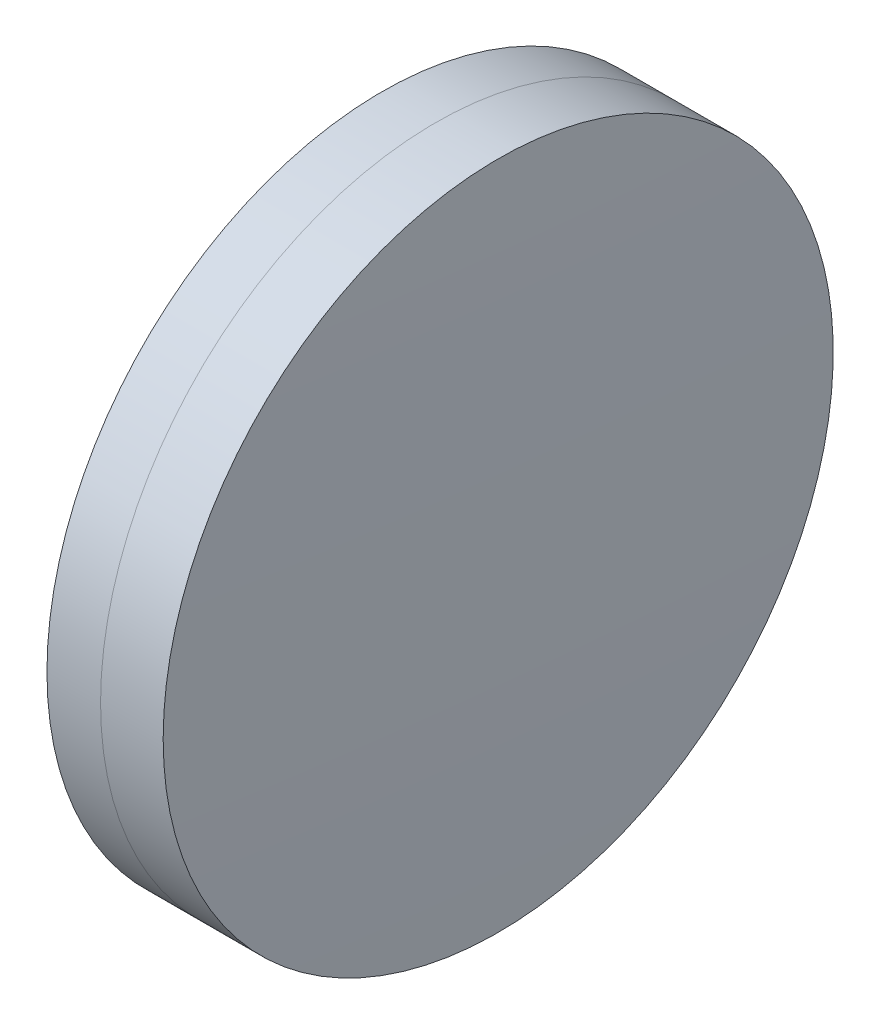
SolidWorks part; units mm, degrees
ref_plane "前视基准面" through (0, 0, 0) normal (0, 0, 1) x (1, 0, 0)
ref_plane "上视基准面" through (0, 0, 0) normal (0, 1, 0) x (1, 0, 0)
ref_plane "右视基准面" through (0, 0, 0) normal (1, 0, 0) x (0, 0, -1)
sketch "草图1" plane through (0, 0, 0) normal (0, 1, 0) x (1, 0, 0)
  line L0 (-9.7026, 0) -> (186.8214, 0) construction
  line L1 (174.7879, -12.5) -> (176.7879, -12.5)
  line L2 (174.7879, 12.5) -> (176.7879, 12.5)
  arc A0 (176.7879, -12.5) -> (176.7879, 12.5) centre (14.8797, 0) ccw
  arc A1 (174.7879, 12.5) -> (174.7879, -12.5) centre (420.1097, 0) ccw
  point P4 (181.7826, 0)
  point P6 (186.8214, 0)
  point P10 (174.4697, 0)
  point P11 (177.2697, 0)
  dimension "D3" = 245.64
  dimension "D4" = 162.39
  dimension "D1" = 12.5
  dimension "D2" = 12.5
  dimension "D5" = 2.8
revolve "旋转1" add sketch "草图1" angle 360 about L0
sketch "草图2" plane through (0, 0, 0) normal (0, 1, 0) x (1, 0, 0)
  line L0 (-0.5519, 0) -> (189.1497, 0) construction
  line L2 (176.7879, 12.5) -> (179.1238, 12.5)
  line L3 (176.7879, -12.5) -> (179.1238, -12.5)
  arc A0 (179.1238, -12.5) -> (179.1238, 12.5) centre (-356.5503, 0) ccw
  arc A1 (176.7879, -12.5) -> (176.7879, 12.5) centre (14.8797, 0) ccw construction
  arc A2 (176.7879, -12.5) -> (176.7879, 12.5) centre (14.8797, 0) ccw
  point P4 (177.2697, 0)
  point P8 (179.2697, 0)
  point P9 (189.1497, 0)
  dimension "D1" = 535.82
  dimension "D2" = 2
revolve "旋转3" add sketch "草图2" angle 360 about L0
